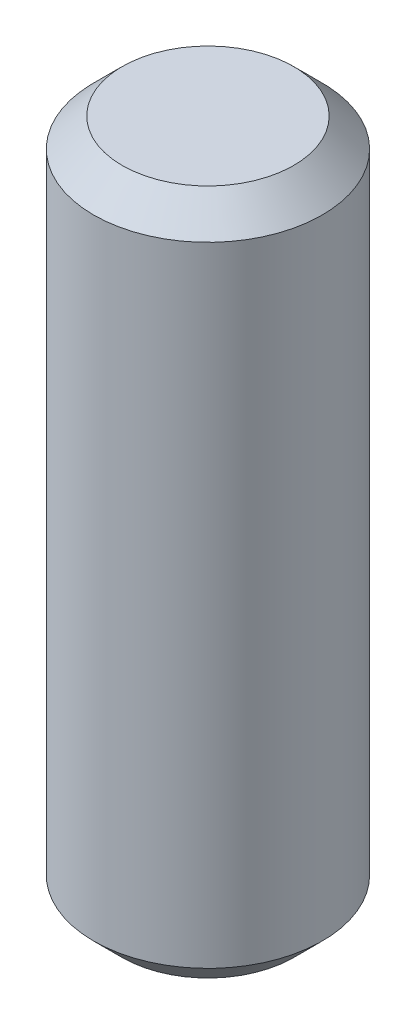
SolidWorks part; units mm, degrees
material "7075-T6 (SN)"
ref_plane "Front Plane" through (0, 0, 0) normal (0, 0, 1) x (1, 0, 0)
ref_plane "Top Plane" through (0, 0, 0) normal (0, 1, 0) x (1, 0, 0)
ref_plane "Right Plane" through (0, 0, 0) normal (1, 0, 0) x (0, 0, -1)
sketch "Sketch1" plane through (0, 0, 0) normal (0, 1, 0) x (1, 0, 0)
  circle A0 centre (0, 0) radius 2
  dimension "D1" = 4
extrude "Boss-Extrude1" add sketch "Sketch1" along normal blind 12
chamfer "Chamfer1" distance 0.5 angle 45 2 edges at (0, 12, 2) (0, 0, 2)
